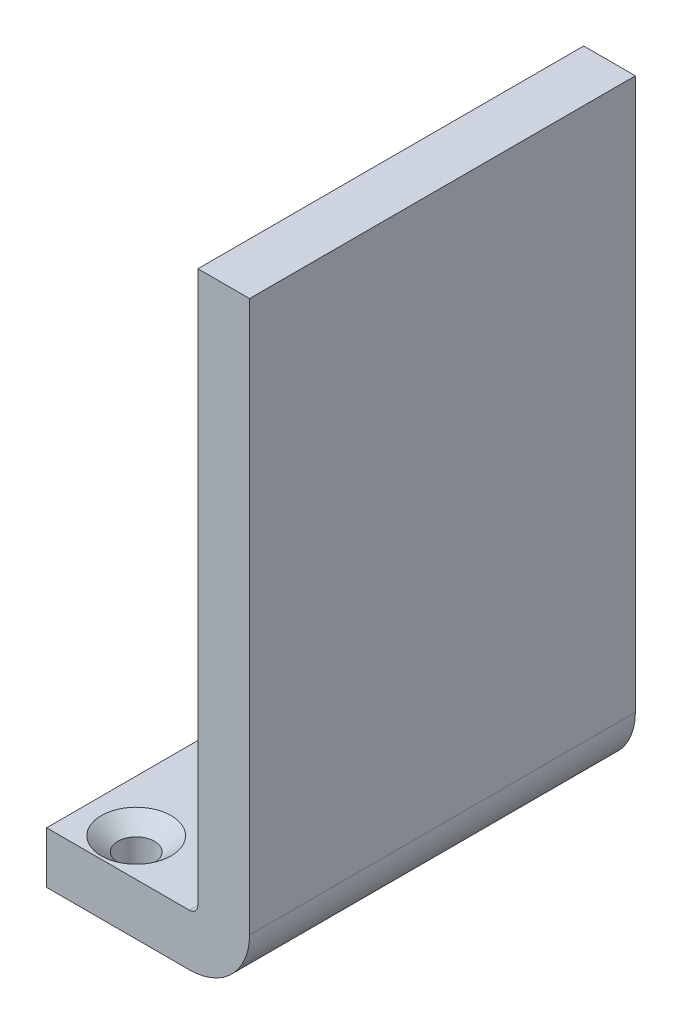
SolidWorks part; units mm, degrees
ref_plane "Front Plane" through (0, 0, 0) normal (0, 0, 1) x (1, 0, 0)
ref_plane "Top Plane" through (0, 0, 0) normal (0, 1, 0) x (1, 0, 0)
ref_plane "Right Plane" through (0, 0, 0) normal (1, 0, 0) x (0, 0, -1)
sketch "Sketch1" plane through (0, 0, 0) normal (0, 1, 0) x (1, 0, 0)
  line L0 (9.525, 73.66) -> (9.525, 2.54) construction
  line L1 (0, 2.54) -> (25.4, 2.54)
  line L2 (0, 2.54) -> (0, 73.66)
  line L3 (0, 73.66) -> (25.4, 73.66)
  line L4 (25.4, 2.54) -> (25.4, 73.66)
  circle A0 centre (9.525, 45.4406) radius 3.175 construction
  circle A1 centre (9.525, 34.925) radius 3.175 construction
  circle A2 centre (9.525, 9.525) radius 3.175 construction
  circle A3 centre (9.525, 66.3194) radius 3.175 construction
extrude "Boss-Extrude1" add sketch "Sketch1" along normal blind 9.525
hole_wizard "CSK for 1/4 Flat Head Machine Screw (100)1" positions "Sketch3" profile "Sketch2" countersink size "1/4" standard "ANSI Inch" end condition through all
sketch "Sketch3" plane through (0, 9.525, 0) normal (0, 1, 0) x (1, 0, 0)
  point P0 (9.525, 9.525)
  point P4 (9.525, 34.925)
  point P7 (9.525, 45.4406)
  point P10 (9.525, 66.3194)
sketch "Sketch2" plane through (9.525, 9.525, -9.525) normal (1, 0, 0) x (0, 0, 1)
  line L0 (0, 0) -> (0, 9.525)
  line L1 (0, 9.525) -> (3.3782, 9.525)
  line L2 (3.3782, 9.525) -> (3.3782, 2.5682)
  line L3 (3.3782, 2.5682) -> (6.4389, 0)
  line L5 (6.4389, 0) -> (0, 0)
  line L6 (-3.3782, 2.5682) -> (-6.4389, 0) construction
  line L11 (0, -6.35) -> (0, 107.95) construction
  dimension "Thru Hole Dia." = 6.7564
  dimension "Thru Hole Depth" = 9.525
  dimension "Near C'Sink Dia." = 12.8778
  dimension "Near C'Sink Angle" = 100
sketch "Sketch4" plane through (0, 0, -73.66) normal (0, 0, -1) x (-1, 0, 0)
  line L1 (-32.6434, 11.1125) -> (-32.6434, 112.7125)
  line L2 (-25.4, 4.7625) -> (-26.2934, 4.7625)
  line L3 (-25.4, 9.525) -> (-25.4, 0) construction
  arc A0 (-26.2934, 4.7625) -> (-32.6434, 11.1125) centre (-26.2934, 11.1125) cw
  dimension "D1" = 6.35
sketch "Sketch6" plane through (25.4, 0, 0) normal (1, 0, 0) x (0, 0, -1)
  line L1 (2.54, 9.525) -> (73.66, 9.525)
  line L2 (2.54, 9.525) -> (2.54, 0)
  line L3 (2.54, 0) -> (73.66, 0)
  line L4 (73.66, 9.525) -> (73.66, 0)
sweep "Sweep1" add profiles "Sketch6" path "Sketch4"
